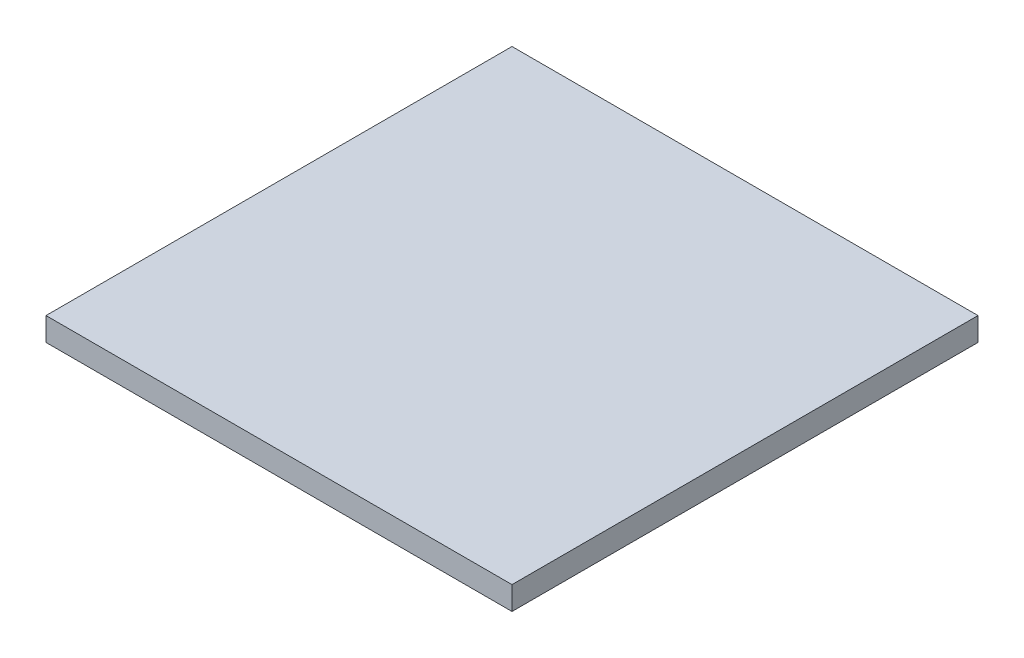
SolidWorks part; units mm, degrees
ref_plane "Front Plane" through (0, 0, 0) normal (0, 0, 1) x (1, 0, 0)
ref_plane "Top Plane" through (0, 0, 0) normal (0, 1, 0) x (1, 0, 0)
ref_plane "Right Plane" through (0, 0, 0) normal (1, 0, 0) x (0, 0, -1)
sketch "Sketch1" plane through (0, 0, 0) normal (0, 1, 0) x (1, 0, 0)
  line L1 (-200, -200) -> (200, -200)
  line L2 (-200, -200) -> (-200, 200)
  line L3 (-200, 200) -> (200, 200)
  line L4 (200, -200) -> (200, 200)
  line L5 (0, 200) -> (0, -200) construction
  line L6 (-200, 0) -> (200, 0) construction
  point P0 (0, 0)
  dimension "D1" = 400
extrude "Boss-Extrude1" add sketch "Sketch1" along normal blind 20 contours L2 L3 L4 L1
